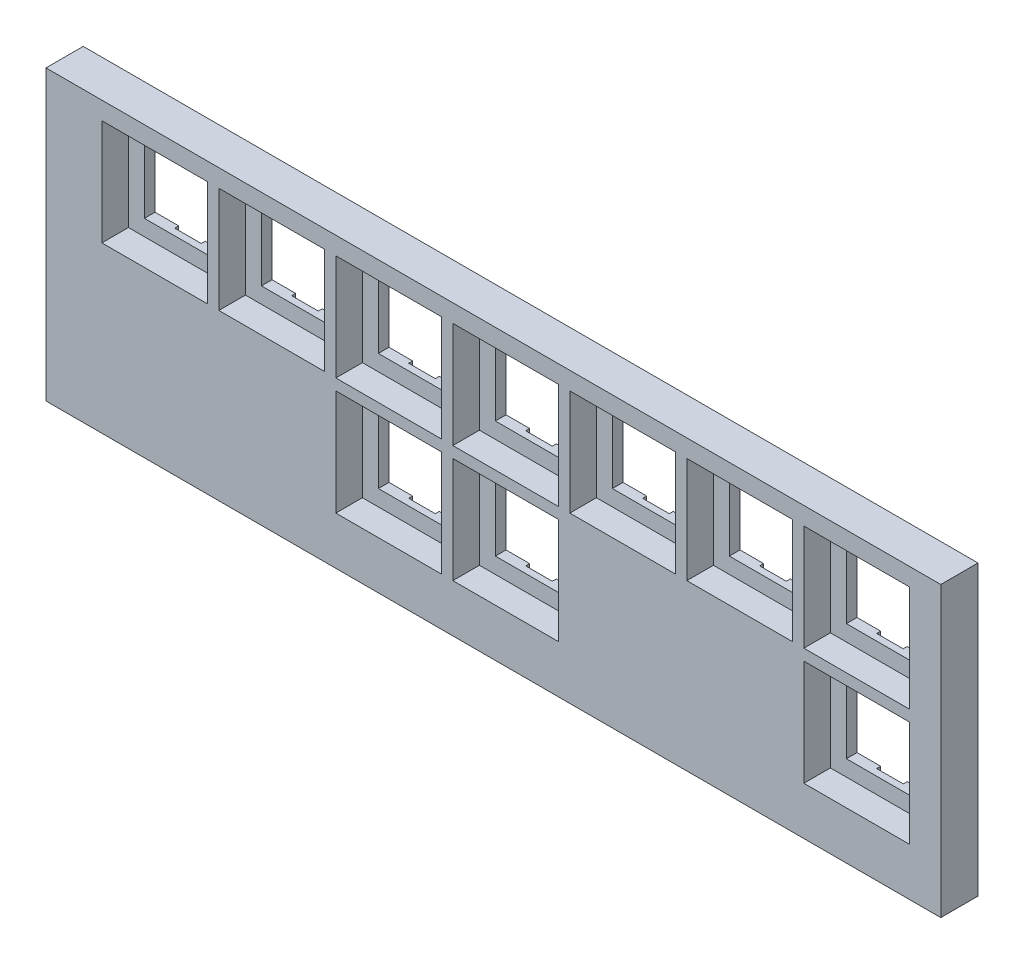
SolidWorks part; units mm, degrees
ref_plane "Front Plane" through (0, 0, 0) normal (0, 0, 1) x (1, 0, 0)
ref_plane "Top Plane" through (0, 0, 0) normal (0, 1, 0) x (1, 0, 0)
ref_plane "Right Plane" through (0, 0, 0) normal (1, 0, 0) x (0, 0, -1)
sketch "Sketch6" plane through (0, 0, 0) normal (0, 0, 1) x (1, 0, 0)
  line L1 (0, 0) -> (168.25, 0)
  line L2 (0, 0) -> (0, 54.25)
  line L3 (0, 54.25) -> (168.25, 54.25)
  line L4 (168.25, 0) -> (168.25, 54.25)
  dimension "D1" = 168.25
  dimension "D2" = 54.25
extrude "Boss-Extrude2" add sketch "Sketch6" along normal blind 7 separate body
sketch "Sketch7" plane through (0, 0, 7) normal (0, 0, 1) x (1, 0, 0)
  line L0 (0, 27.125) -> (168.25, 27.125) construction
  line L1 (10.5, 50.9) -> (30.4, 50.9)
  line L2 (10.5, 50.9) -> (10.5, 31)
  line L3 (10.5, 31) -> (30.4, 31)
  line L4 (30.4, 50.9) -> (30.4, 31)
  line L5 (0, 54.25) -> (0, 0) construction
  line L6 (0, 0) -> (168.25, 0) construction
  line L7 (168.25, 0) -> (168.25, 54.25) construction
  line L10 (20.45, 50.9) -> (20.45, 31) construction
  dimension "D1" = 19.9
  dimension "D2" = 19.9
  dimension "D3" = 10.5
  dimension "D4" = 31
extrude "Cut-Extrude4" cut sketch "Sketch7" against normal blind 5
sketch "Sketch8" plane through (0, 0, 2) normal (0, 0, 1) x (1, 0, 0)
  line L0 (10.5, 40.95) -> (30.4, 40.95) construction
  line L1 (13.5, 47.9) -> (27.4, 47.9)
  line L2 (13.5, 47.9) -> (13.5, 34)
  line L3 (13.5, 34) -> (27.4, 34)
  line L4 (27.4, 47.9) -> (27.4, 34)
  line L5 (10.5, 50.9) -> (10.5, 31) construction
  line L6 (30.4, 31) -> (30.4, 50.9) construction
  line L7 (20.45, 34) -> (20.45, 47.9) construction
  point P12 (20.45, 40.95)
  point P13 (20.45, 40.95)
  dimension "D1" = 13.9
  dimension "D2" = 13.9
extrude "Cut-Extrude5" cut sketch "Sketch8" against normal blind 4
sketch "Sketch9" plane through (0, 47.9, 0) normal (0, -1, 0) x (-1, 0, 0)
  line L0 (-20.45, -2) -> (-20.45, -0.75) construction
  line L1 (-17.95, -0.75) -> (-22.95, -0.75)
  line L2 (-17.95, -0.75) -> (-17.95, 0)
  line L3 (-17.95, 0) -> (-22.95, 0)
  line L4 (-22.95, -0.75) -> (-22.95, 0)
  line L5 (-27.4, -2) -> (-13.5, -2) construction
  line L6 (-27.4, 0) -> (-13.5, 0) construction
  dimension "D1" = 1.25
  dimension "D2" = 5
extrude "Cut-Extrude6" cut sketch "Sketch9" against normal blind 1
ref_plane "Plane2" through (0, 40.95, 0) normal (0, -1, 0) x (-1, 0, 0)
mirror "Mirror2" about plane through (0, 40.95, 0) normal (0, -1, 0) of "Cut-Extrude6"
pattern_linear "LPattern1" count 7 spacing 22 along (1, 0, 0) count 2 spacing 22 along (0, -1, 0) skipping (0, 1), (1, 1), (4, 1), (5, 1) of "Cut-Extrude4", "Cut-Extrude5", "Cut-Extrude6", "Mirror2"
